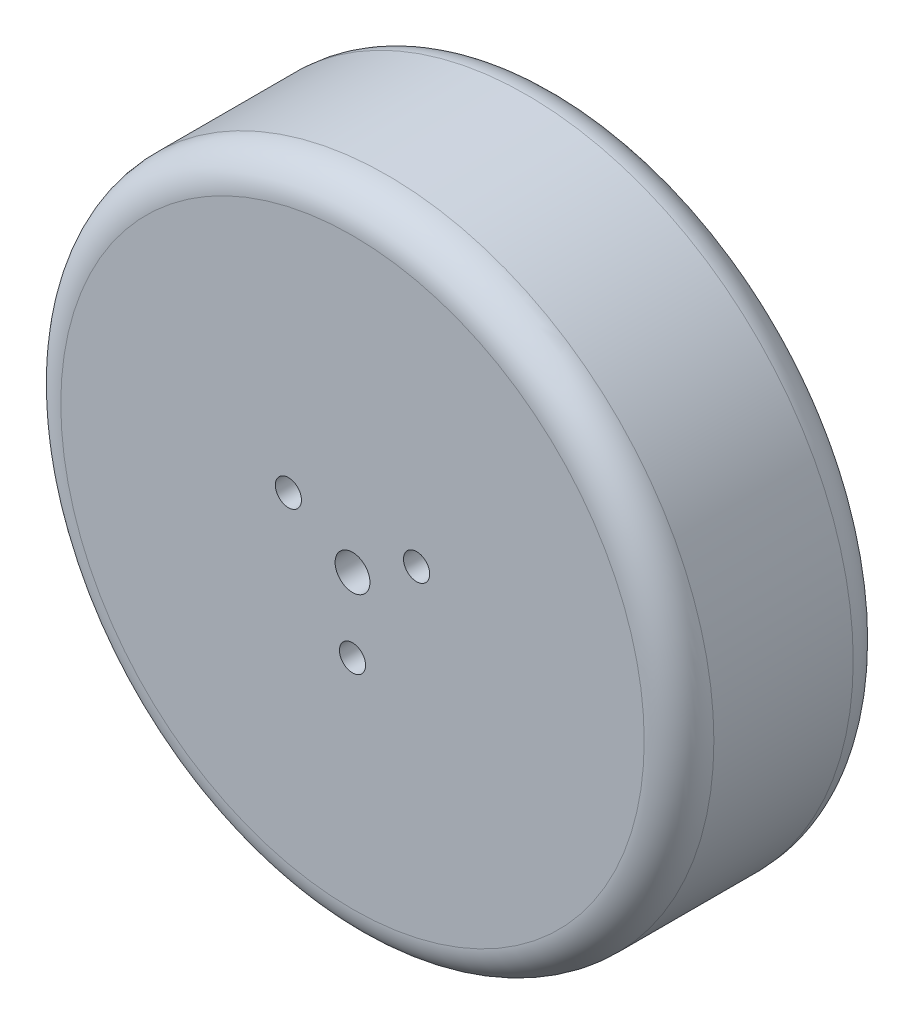
SolidWorks part; units mm, degrees
ref_plane "Front Plane" through (0, 0, 0) normal (0, 0, 1) x (1, 0, 0)
ref_plane "Top Plane" through (0, 0, 0) normal (0, 1, 0) x (1, 0, 0)
ref_plane "Right Plane" through (0, 0, 0) normal (1, 0, 0) x (0, 0, -1)
sketch "Sketch1" plane through (0, 0, 0) normal (0, 0, 1) x (1, 0, 0)
  circle A0 centre (0, 0) radius 37.5
  dimension "D1" = 75
extrude "Boss-Extrude2" add sketch "Sketch1" along normal blind 24
fillet "Fillet1" radius 4 2 edges at (37.5, 0, 0) (37.5, 0, 24)
sketch "Sketch2" plane through (0, 0, 24) normal (0, 0, 1) x (1, 0, 0)
  circle A0 centre (0, 0) radius 2
  dimension "D1" = 4
extrude "Cut-Extrude1" cut sketch "Sketch2" against normal blind 24
sketch "Sketch3" plane through (0, 0, 24) normal (0, 0, 1) x (1, 0, 0)
  line L0 (0, 39.4793) -> (0, -41.875) construction
  circle A0 centre (0, -8.5) radius 1.5
  dimension "D1" = 3
  dimension "D2" = 8.5
extrude "Cut-Extrude3" cut sketch "Sketch3" against normal through all
pattern_circular "CirPattern1" count 3 every 120 about axis through (0, 0, 0) along (0, 0, 1) of "Cut-Extrude3"
